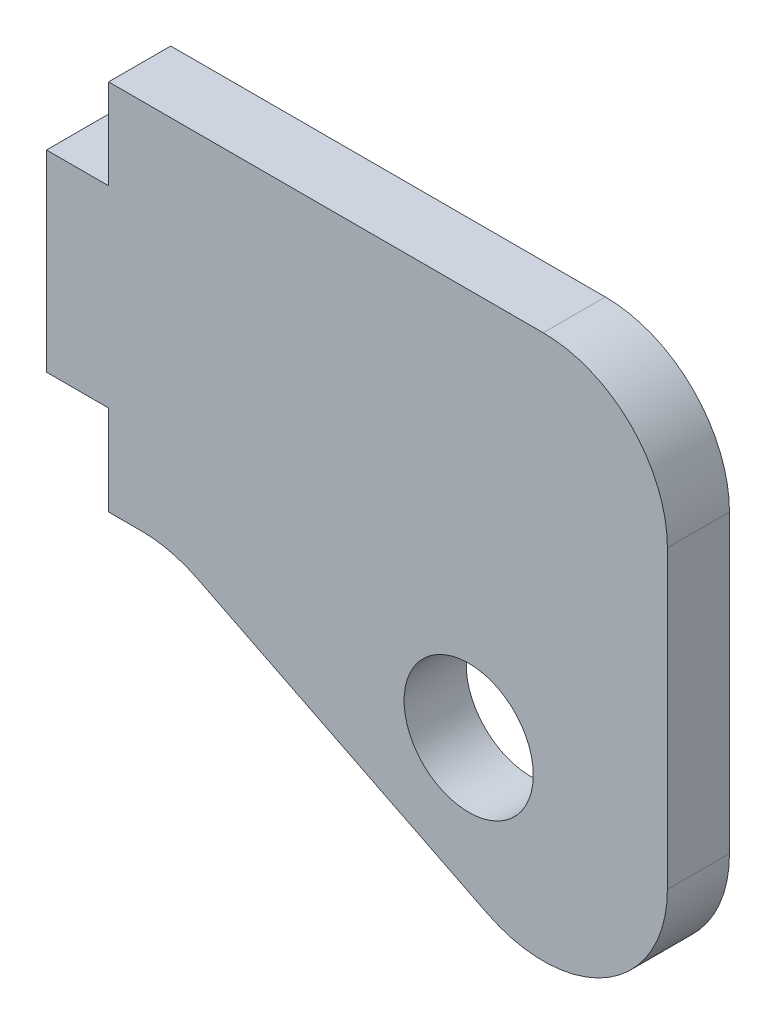
SolidWorks part; units mm, degrees
material "AISI 4340 Steel, normalized"
ref_plane "X-Y Datum" through (0, 0, 0) normal (0, 0, 1) x (1, 0, 0)
ref_plane "X-Z Datum" through (0, 0, 0) normal (0, 1, 0) x (1, 0, 0)
ref_plane "Y-Z Datum" through (0, 0, 0) normal (1, 0, 0) x (0, 0, -1)
sketch "Sketch1" plane through (0, 0, 0) normal (0, 0, 1) x (1, 0, 0)
  line L0 (0, -9.525) -> (6.35, -9.525)
  line L2 (0, 9.525) -> (0, -9.525)
  line L5 (6.35, -9.525) -> (31.75, -22.225)
  line L6 (31.75, -22.225) -> (31.75, 9.525)
  line L7 (31.75, 9.525) -> (0, 9.525)
  point P1 (17.1085, 7.9375)
  point P5 (0, 0)
  point P8 (7.6146, -7.9375)
  point P9 (0, 0)
  point P10 (14.659, -9.525)
  point P11 (38.1, -17.8212)
  point P12 (0, -9.4239)
  point P13 (0, 0)
  point P14 (0, -12.9445)
  point P15 (0, -9.967)
  point P16 (0, 7.5783)
  dimension "D1" = 19.05
  dimension "D2" = 31.75
  dimension "D3" = 6.35
  dimension "D4" = 31.75
extrude "Boss-Extrude1" add sketch "Sketch1" along normal blind 3.175
fillet "Fillet1" radius 6.35 3 edges at (31.75, 9.525, 1.5875) (31.75, -22.225, 1.5875) (6.35, -9.525, 1.5875)
sketch "Sketch3" plane through (0, 0, 3.175) normal (0, 0, 1) x (1, 0, 0)
  circle A0 centre (21.5883, -10.3159) radius 3.302
  point P3 (21.7443, -10.2104)
  dimension "D1" = 6.604
extrude "Cut-Extrude1" cut sketch "Sketch3" against normal blind 3.175
sketch "Sketch4" plane through (0, 0, 3.175) normal (0, 0, 1) x (1, 0, 0)
  line L0 (0, 9.525) -> (0, -9.525) construction
  line L5 (0, 9.525) -> (3.175, 9.525)
  line L6 (0, 9.525) -> (0, 4.9213)
  line L7 (0, 4.9213) -> (3.175, 4.9213)
  line L8 (3.175, 9.525) -> (3.175, 4.9213)
  line L10 (0, -9.525) -> (3.175, -9.525)
  line L11 (0, -9.525) -> (0, -4.9213)
  line L12 (0, -4.9213) -> (3.175, -4.9213)
  line L13 (3.175, -9.525) -> (3.175, -4.9213)
  dimension "D1" = 3.175
  dimension "D2" = 3.175
  dimension "D3" = 9.8425
extrude "Cut-Extrude2" cut sketch "Sketch4" against normal blind 3.175
